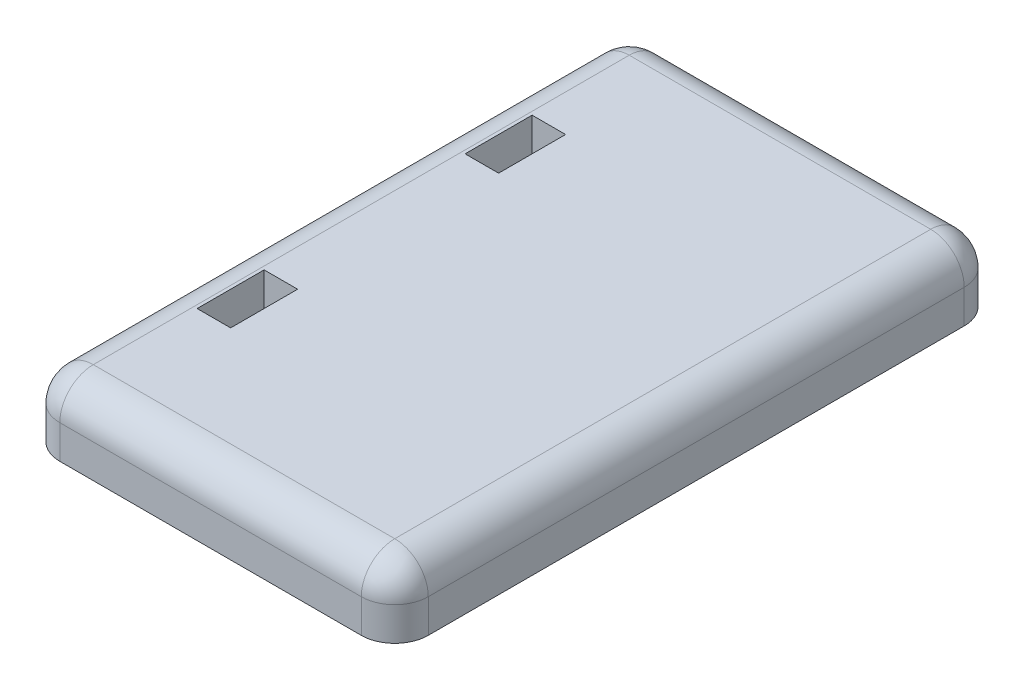
SolidWorks part; units mm, degrees
ref_plane "前视基准面" through (0, 0, 0) normal (0, 0, 1) x (1, 0, 0)
ref_plane "上视基准面" through (0, 0, 0) normal (0, 1, 0) x (1, 0, 0)
ref_plane "右视基准面" through (0, 0, 0) normal (1, 0, 0) x (0, 0, -1)
other "Configuration Table"
sketch "草图2" plane through (0, 0, 0) normal (0, 1, 0) x (1, 0, 0)
  line L1 (-27.5, -45) -> (27.5, -45)
  line L2 (-27.5, -45) -> (-27.5, 45)
  line L3 (-27.5, 45) -> (27.5, 45)
  line L4 (27.5, -45) -> (27.5, 45)
  line L5 (-27.5, -45) -> (27.5, 45) construction
  line L6 (-27.5, 45) -> (27.5, -45) construction
  point P0 (0, 0)
  dimension "D1" = 90
  dimension "D2" = 55
extrude "凸台-拉伸1" add sketch "草图2" along normal blind 10
fillet "圆角1" radius 5 1 edges at (-27.5, 10, 0)
fillet "圆角2" radius 5 3 edges at (-27.5, 2.5, -45) (-26.0355, 8.5355, -45) (2.5, 10, -45)
fillet "圆角3" radius 5 3 edges at (27.5, 2.5, -45) (27.5, 8.5355, -43.5355) (27.5, 10, 2.5)
fillet "圆角4" radius 5 5 edges at (-27.5, 2.5, 45) (-26.0355, 8.5355, 45) (27.5, 2.5, 45) (26.0355, 8.5355, 45) (0, 10, 45)
sketch "草图3" plane through (0, 10, 0) normal (0, 1, 0) x (1, 0, 0)
  line L1 (-22, 25) -> (-17, 25)
  line L2 (-22, 25) -> (-22, 15)
  line L3 (-22, 15) -> (-17, 15)
  line L4 (-17, 25) -> (-17, 15)
  line L5 (-22, 25) -> (-17, 15) construction
  line L6 (-22, 15) -> (-17, 25) construction
  line L7 (-22, -15) -> (-17, -15)
  line L8 (-22, -15) -> (-22, -25)
  line L9 (-22, -25) -> (-17, -25)
  line L10 (-17, -15) -> (-17, -25)
  line L11 (-22, -15) -> (-17, -25) construction
  line L12 (-22, -25) -> (-17, -15) construction
  point P0 (-19.5, 20)
  point P5 (-19.5, -20)
  dimension "D1" = 5
  dimension "D2" = 10
  dimension "D3" = 5
  dimension "D4" = 10
  dimension "D5" = 15
  dimension "D6" = 15
  dimension "D7" = 17
extrude "切除-拉伸1" cut sketch "草图3" against normal blind 5 contours L4 L1 L2 L3 | L8 L7 L10 L9
